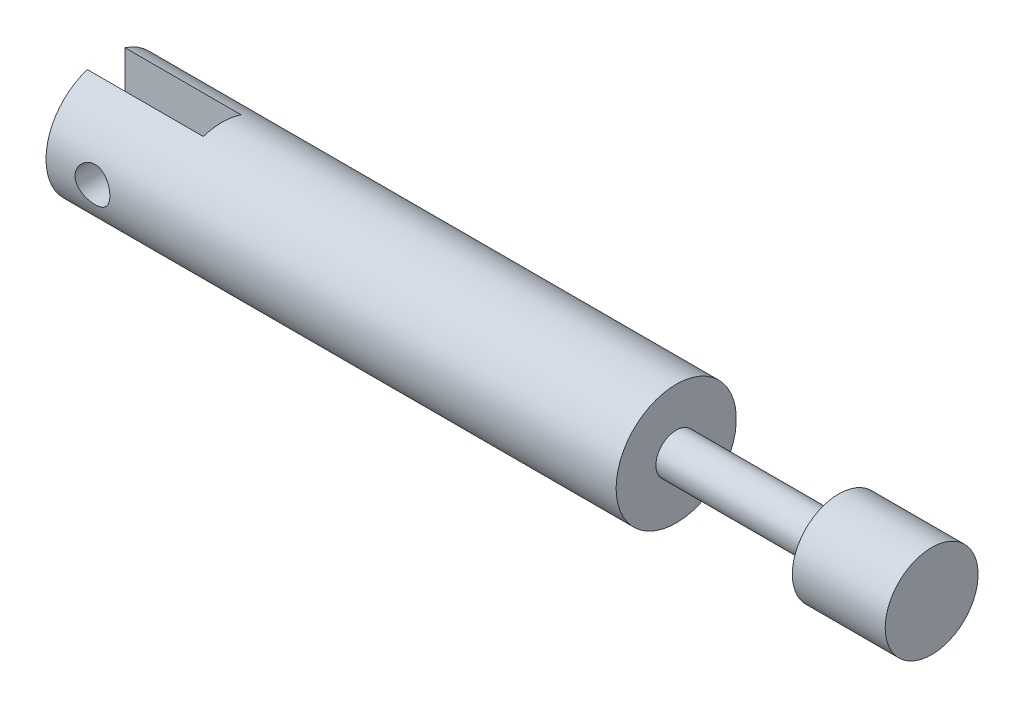
SolidWorks part; units mm, degrees
ref_plane "Front Plane" through (0, 0, 0) normal (0, 0, 1) x (1, 0, 0)
ref_plane "Top Plane" through (0, 0, 0) normal (0, 1, 0) x (1, 0, 0)
ref_plane "Right Plane" through (0, 0, 0) normal (1, 0, 0) x (0, 0, -1)
sketch "Sketch1" plane through (0, 0, 0) normal (0, 0, 1) x (1, 0, 0)
  line L1 (0, 0) -> (71.1, 0)
  line L2 (0, 0) -> (0, 5.175)
  line L3 (0, 5.175) -> (71.1, 5.175)
  line L4 (71.1, 0) -> (71.1, 5.175)
  line L5 (71.1, 0) -> (63.1, 0)
  line L6 (71.1, 0) -> (71.1, 4)
  line L7 (71.1, 4) -> (63.1, 4)
  line L8 (63.1, 0) -> (63.1, 4)
  line L9 (63.1, 0) -> (49.1, 0)
  line L10 (63.1, 0) -> (63.1, 1.75)
  line L11 (63.1, 1.75) -> (49.1, 1.75)
  line L12 (49.1, 0) -> (49.1, 1.75)
  line L13 (0, 0) -> (49.1, 0)
  line L14 (0, 0) -> (0, 5.175)
  line L15 (0, 5.175) -> (49.1, 5.175)
  line L16 (49.1, 0) -> (49.1, 5.175)
  point P2 (0, 2.5875)
  dimension "D1" = 71.1
  dimension "D2" = 5.175
  dimension "D3" = 8
  dimension "D4" = 4
  dimension "D5" = 1.75
  dimension "D6" = 14
  dimension "D7" = 49.1
revolve "Revolve1" add sketch "Sketch1" angle 360 about L1
ref_plane "Plane1" through (0, 0, 5.175) normal (0, 0, 1) x (1, 0, 0)
sketch "Sketch2" plane through (0, 0, 5.175) normal (0, 0, 1) x (1, 0, 0)
  line L0 (0, 5.175) -> (0, -5.175) construction
  line L1 (49.1, 5.175) -> (0, 5.175) construction
  circle A0 centre (4, 0) radius 1.5
  dimension "D1" = 3
  dimension "D2" = 4
  dimension "D3" = 5.175
extrude "Cut-Extrude1" cut sketch "Sketch2" against normal up to next
sketch "Sketch3" plane through (0, 0, 0) normal (-1, 0, 0) x (0, 0, 1)
  line L1 (-1.625, -5.175) -> (1.625, -5.175)
  line L2 (-1.625, -5.175) -> (-1.625, 5.175)
  line L3 (-1.625, 5.175) -> (1.625, 5.175)
  line L4 (1.625, -5.175) -> (1.625, 5.175)
  line L5 (-1.625, -5.175) -> (1.625, 5.175) construction
  line L6 (-1.625, 5.175) -> (1.625, -5.175) construction
  point P0 (0, 0)
  dimension "D1" = 3.25
  dimension "D2" = 10.35
extrude "Cut-Extrude2" cut sketch "Sketch3" against normal blind 10
